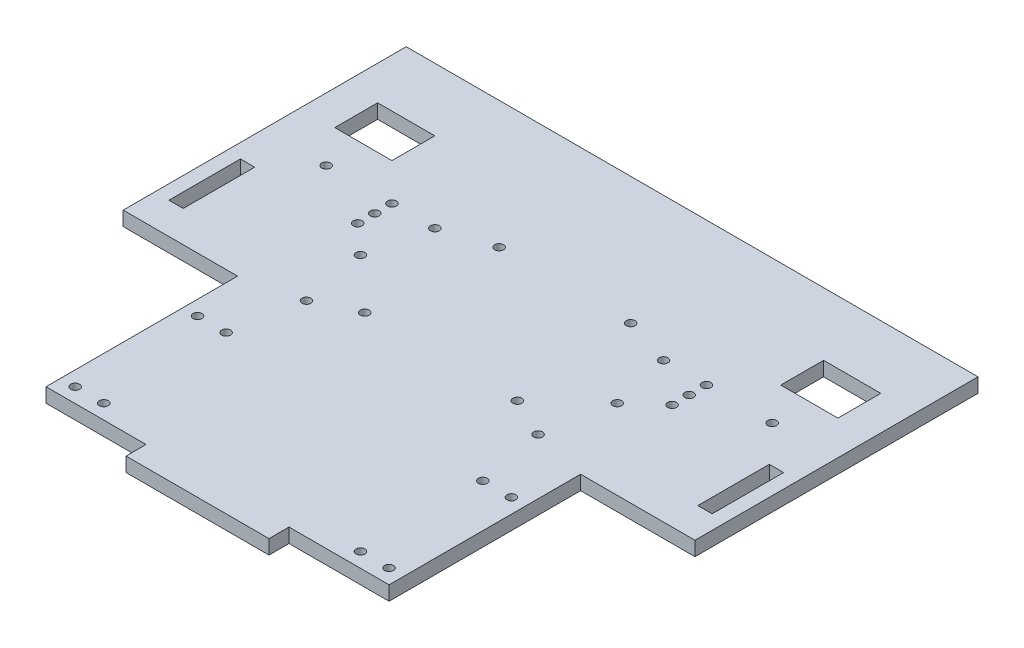
SolidWorks part; units mm, degrees
ref_plane "Front Plane" through (0, 0, 0) normal (0, 0, 1) x (1, 0, 0)
ref_plane "Top Plane" through (0, 0, 0) normal (0, 1, 0) x (1, 0, 0)
ref_plane "Right Plane" through (0, 0, 0) normal (1, 0, 0) x (0, 0, -1)
sketch "Sketch1" plane through (0, 0, 0) normal (0, 1, 0) x (1, 0, 0)
  line L6 (-25, -75) -> (25, -75)
  line L16 (25, -75) -> (25, -68)
  line L18 (-25, -75) -> (-25, -68)
  line L28 (-160.3351, 0) -> (160.3351, 0) construction
  line L29 (-100, 98) -> (-100, 0)
  line L30 (100, 98) -> (100, 0)
  line L33 (-100, 0) -> (-100, -1)
  line L34 (-100, -1) -> (-60, -1)
  line L35 (-60, -1) -> (-60, -68)
  line L36 (-60, -68) -> (-25, -68)
  line L37 (0, -68) -> (0, 68) construction
  line L38 (60, -68) -> (25, -68)
  line L39 (60, -1) -> (60, -68)
  line L40 (100, -1) -> (60, -1)
  line L41 (100, 0) -> (100, -1)
  line L43 (-100, 98) -> (100, 98)
  line L44 (-88, 61) -> (-68, 61)
  line L45 (-88, 61) -> (-88, 76)
  line L46 (-88, 76) -> (-68, 76)
  line L47 (-68, 61) -> (-68, 76)
  line L48 (-88, 61) -> (-68, 76) construction
  line L49 (-88, 76) -> (-68, 61) construction
  line L50 (88, 76) -> (68, 76)
  line L51 (68, 61) -> (68, 76)
  line L52 (88, 61) -> (68, 61)
  line L53 (88, 61) -> (88, 76)
  line L55 (-95, 35) -> (-90, 35)
  line L56 (-95, 35) -> (-95, 10)
  line L57 (-95, 10) -> (-90, 10)
  line L58 (-90, 35) -> (-90, 10)
  line L59 (-95, 35) -> (-90, 10) construction
  line L60 (-95, 10) -> (-90, 35) construction
  line L61 (95, 10) -> (90, 10)
  line L62 (90, 35) -> (90, 10)
  line L63 (95, 35) -> (90, 35)
  line L64 (95, 35) -> (95, 10)
  circle A0 centre (-78, 48) radius 1.55
  circle A1 centre (78, 48) radius 1.55
  circle A2 centre (-40, 48) radius 1.55
  circle A3 centre (40, 48) radius 1.55
  circle A8 centre (-44.9, 26.9) radius 1.55
  circle A9 centre (44.9, 26.9) radius 1.55
  circle A11 centre (-44.9, -62.9) radius 1.55
  circle A12 centre (-44.9, -20.1) radius 1.55
  circle A13 centre (-54.9, -62.9) radius 1.55
  circle A14 centre (-54.9, -20.1) radius 1.55
  circle A15 centre (44.9, -62.9) radius 1.55
  circle A16 centre (54.9, -62.9) radius 1.55
  circle A17 centre (44.9, -20.1) radius 1.55
  circle A18 centre (54.9, -20.1) radius 1.55
  circle A19 centre (-55, 48) radius 1.55
  circle A20 centre (55, 48) radius 1.55
  circle A21 centre (-26.7, 10.2) radius 1.55
  circle A22 centre (26.7, 10.2) radius 1.55
  circle A23 centre (-40.5, 3.6055) radius 1.55
  circle A24 centre (40.5, 3.6055) radius 1.55
  circle A25 centre (-23, 53.5) radius 1.55
  circle A26 centre (23, 53.5) radius 1.55
  circle A31 centre (-55, 42) radius 1.55
  circle A32 centre (-55, 36) radius 1.55
  circle A33 centre (55, 36) radius 1.55
  circle A34 centre (55, 42) radius 1.55
  point P2 (0, -18)
  point P4 (0, 0)
  point P6 (-92.5, 22.5)
  point P21 (0, 0)
  point P34 (-78, 68.5)
  point P47 (0, -18)
  point P54 (0, -18)
  point P55 (0, -18)
  point P57 (0, -18)
  point P59 (0, -18)
  point P60 (0, -18)
  point P63 (0, -18)
  point P64 (0, -18)
  point P67 (0, -18)
  point P84 (0, 0)
  point P85 (-23, 53.5)
  point P101 (-51, 43)
  dimension "D8" = 3.1
  dimension "D9" = 22
  dimension "D11" = 98
  dimension "D21" = 3.1
  dimension "D22" = 42.8
  dimension "D25" = 3.1
  dimension "D26" = 23
  dimension "D28" = 3.1
  dimension "D32" = 3.1
  dimension "D33" = 40.5
  dimension "D37" = 3.1
  dimension "D34" = 6
  dimension "D35" = 3.1
  dimension "D36" = 3.1
  dimension "D3" = 40
  dimension "D4" = 50
  dimension "D5" = 1
  dimension "D6" = 7
  dimension "D7" = 7
  dimension "D10" = 5
  dimension "D12" = 50
  dimension "D14" = 100
  dimension "D15" = 5
  dimension "D16" = 25
  dimension "D17" = 10
  dimension "D18" = 13
  dimension "D19" = 15
  dimension "D20" = 20
  dimension "D23" = 0
  dimension "D24" = 38
  dimension "D27" = 73.3
  dimension "D29" = 87.8
  dimension "D30" = 68
  dimension "D31" = 6
extrude "Boss-Extrude2" add sketch "Sketch1" along normal blind 5
